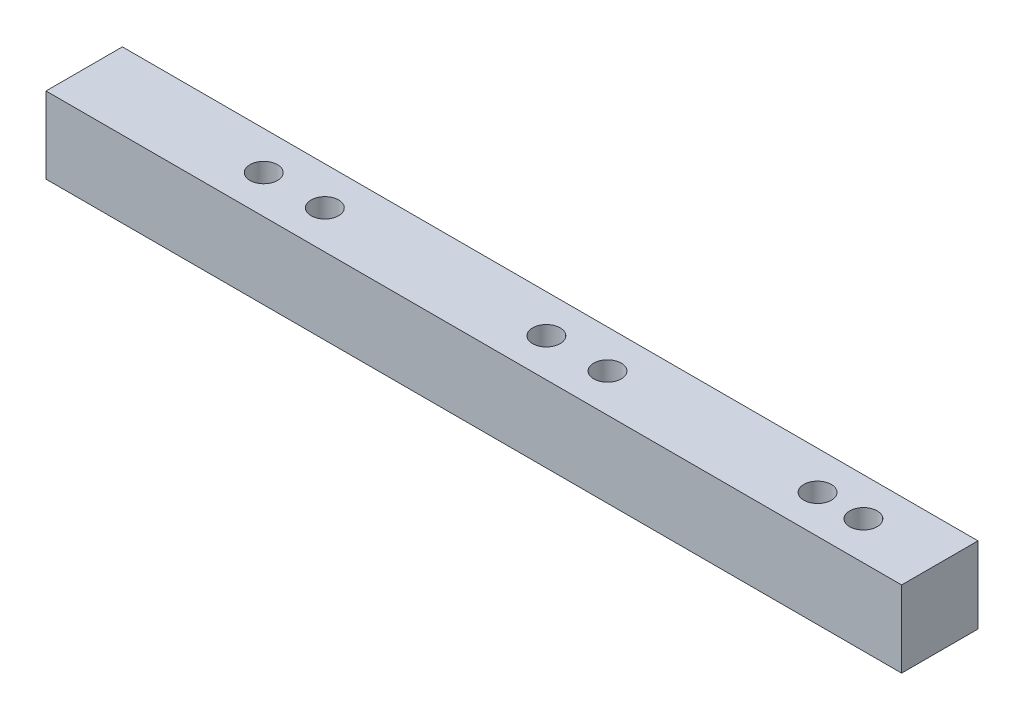
SolidWorks part; units mm, degrees
ref_plane "Front Plane" through (0, 0, 0) normal (0, 0, 1) x (1, 0, 0)
ref_plane "Top Plane" through (0, 0, 0) normal (0, 1, 0) x (1, 0, 0)
ref_plane "Right Plane" through (0, 0, 0) normal (1, 0, 0) x (0, 0, -1)
sketch "Sketch2" plane through (0, 0, 0) normal (0, 0, 1) x (1, 0, 0)
  line L1 (-35.56, 0) -> (35.56, 0)
  line L2 (-35.56, 0) -> (-35.56, 6.35)
  line L3 (-35.56, 6.35) -> (35.56, 6.35)
  line L4 (35.56, 0) -> (35.56, 6.35)
  dimension "D1" = 71.12
  dimension "D2" = 6.35
extrude "Boss-Extrude1" add sketch "Sketch2" along normal blind 6.35
sketch "Sketch3" plane through (0, 0, 0) normal (0, 1, 0) x (1, 0, 0)
  line L0 (-35.56, -6.35) -> (-35.56, 0) construction
  line L1 (35.56, -6.35) -> (35.56, 0) construction
  line L2 (35.56, -6.35) -> (-35.56, -6.35) construction
  line L3 (35.56, 0) -> (-35.56, 0) construction
  circle A0 centre (-20.6375, -3.175) radius 1.143
  circle A1 centre (-15.5575, -3.175) radius 1.143
  circle A2 centre (2.8575, -3.175) radius 1.143
  circle A3 centre (7.9375, -3.175) radius 1.143
  circle A4 centre (25.4, -3.175) radius 1.143
  circle A5 centre (29.21, -3.175) radius 1.143
  dimension "D1" = 2.286
  dimension "D2" = 2.286
  dimension "D3" = 2.286
  dimension "D4" = 2.286
  dimension "D10" = 2.286
  dimension "D11" = 2.286
  dimension "D5" = 5.08
  dimension "D6" = 5.08
  dimension "D7" = 14.9225
  dimension "D8" = 27.6225
  dimension "D9" = 3.175
  dimension "D12" = 3.81
  dimension "D13" = 10.16
  dimension "D14" = 3.175
  dimension "D15" = 3.175
extrude "Cut-Extrude2" cut sketch "Sketch3" along normal blind 6.35
